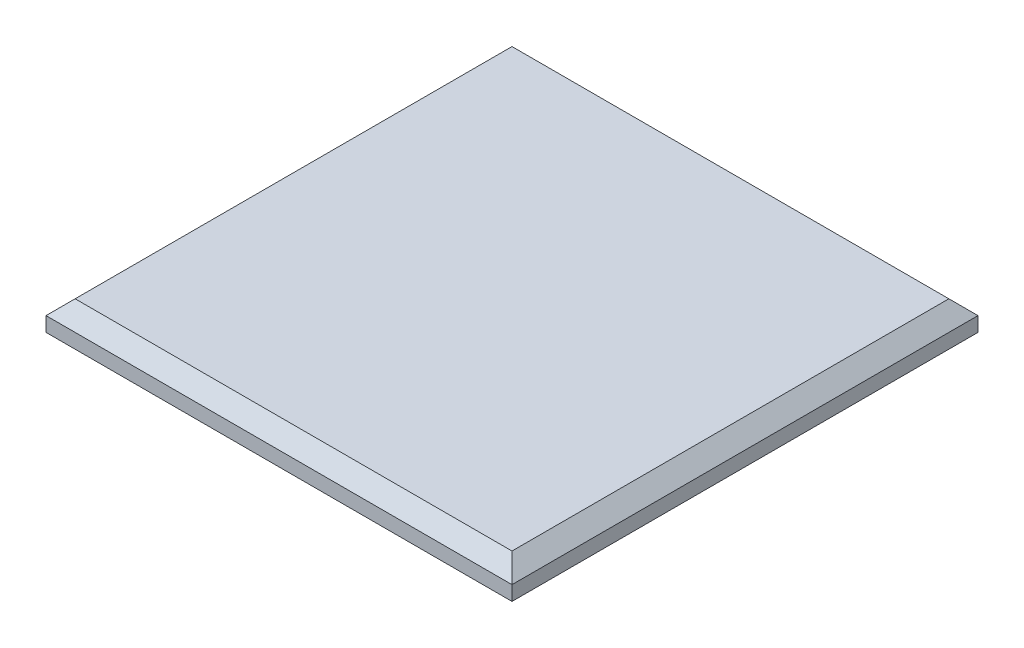
SolidWorks part; units mm, degrees
material "Al - 6061 Polished"
ref_plane "Front Plane" through (0, 0, 0) normal (0, 0, 1) x (1, 0, 0)
ref_plane "Top Plane" through (0, 0, 0) normal (0, 1, 0) x (1, 0, 0)
ref_plane "Right Plane" through (0, 0, 0) normal (1, 0, 0) x (0, 0, -1)
sketch "Sketch1" plane through (0, 0, 0) normal (0, 1, 0) x (1, 0, 0)
  line L2 (-50.8, -50.8) -> (50.8, -50.8)
  line L3 (-50.8, -50.8) -> (-50.8, 50.8)
  line L4 (-50.8, 50.8) -> (50.8, 50.8)
  line L5 (50.8, -50.8) -> (50.8, 50.8)
  line L6 (-50.8, -50.8) -> (50.8, 50.8) construction
  line L7 (-50.8, 50.8) -> (50.8, -50.8) construction
  point P2 (0, 0)
  dimension "D1" = 101.6
extrude "Boss-Extrude1" add sketch "Sketch1" along normal blind 9.525
sketch "Sketch2" plane through (0, 0, 0) normal (0, -1, 0) x (1, 0, 0)
  line L0 (47.498, 47.498) -> (-47.498, 47.498)
  line L1 (-47.498, 47.498) -> (-47.498, -47.498)
  line L2 (-47.498, -47.498) -> (47.498, -47.498)
  line L3 (47.498, -47.498) -> (47.498, 47.498)
  line L4 (50.8, -50.8) -> (50.8, 50.8)
  line L5 (50.8, 50.8) -> (-50.8, 50.8)
  line L6 (-50.8, 50.8) -> (-50.8, -50.8)
  line L7 (-50.8, -50.8) -> (50.8, -50.8)
  line L8 (50.8, -50.8) -> (50.8, 50.8)
  line L9 (50.8, 50.8) -> (-50.8, 50.8)
  line L10 (-50.8, 50.8) -> (-50.8, -50.8)
  line L11 (-50.8, -50.8) -> (50.8, -50.8)
  dimension "D1" = 0
  dimension "D2" = 3.302
extrude "Cut-Extrude1" cut sketch "Sketch2" against normal blind 3.175
chamfer "Chamfer1" distance 3.175 angle 45 4 edges at (0, 9.525, 50.8) (-50.8, 9.525, 0) (0, 9.525, -50.8) (50.8, 9.525, 0)
